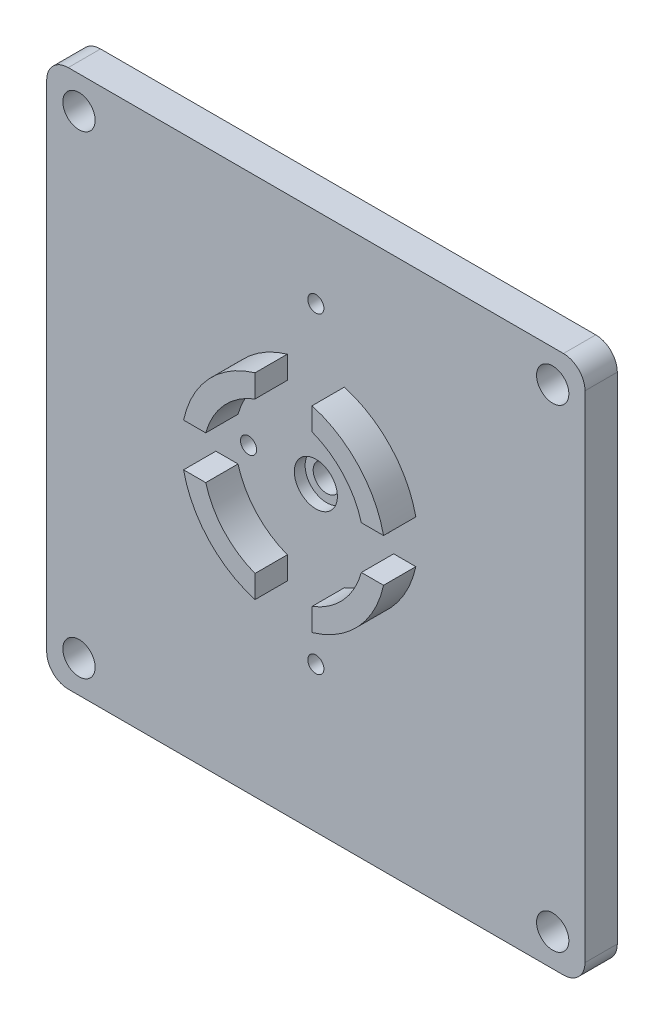
SolidWorks part; units mm, degrees
ref_plane "前视基准面" through (0, 0, 0) normal (0, 0, 1) x (1, 0, 0)
ref_plane "上视基准面" through (0, 0, 0) normal (0, 1, 0) x (1, 0, 0)
ref_plane "右视基准面" through (0, 0, 0) normal (1, 0, 0) x (0, 0, -1)
sketch "草图1" plane through (0, 0, 0) normal (0, 0, 1) x (1, 0, 0)
  line L0 (0, 0) -> (-22, 22) construction
  line L1 (-23, 25) -> (23, 25)
  line L2 (-25, 23) -> (-25, -23)
  line L3 (-23, -25) -> (23, -25)
  line L4 (25, 23) -> (25, -23)
  line L5 (-25, 25) -> (25, -25) construction
  line L6 (-25, -25) -> (25, 25) construction
  circle A0 centre (-22, 22) radius 1.5
  arc A1 (-25, -23) -> (-23, -25) centre (-23, -23) ccw
  arc A2 (23, -25) -> (25, -23) centre (23, -23) ccw
  arc A3 (23, 25) -> (25, 23) centre (23, 23) cw
  arc A4 (-23, 25) -> (-25, 23) centre (-23, 23) ccw
  circle A5 centre (22, 22) radius 1.5
  circle A6 centre (22, -22) radius 1.5
  circle A7 centre (-22, -22) radius 1.5
  point P0 (0, 0)
  dimension "D3" = 3
  dimension "D4" = 3
  dimension "D5" = 2
  dimension "D7" = 3
  dimension "D1" = 50
  dimension "D2" = 50
  dimension "D6" = 4
extrude "凸台-拉伸1" add sketch "草图1" along normal blind 3
sketch "草图2" plane through (0, 0, 3) normal (0, 0, 1) x (1, 0, 0)
  line L1 (-2.65, 14) -> (2.65, 14)
  line L2 (-2.65, 14) -> (-2.65, -8)
  line L3 (-2.65, -8) -> (2.65, -8)
  line L4 (2.65, 14) -> (2.65, -8)
  line L5 (-2.65, 14) -> (2.65, -8) construction
  line L6 (-2.65, -8) -> (2.65, 14) construction
  line L7 (-10, 5) -> (10, 5)
  line L8 (-10, 5) -> (-10, 1)
  line L9 (-10, 1) -> (10, 1)
  line L10 (10, 5) -> (10, 1)
  line L11 (-10, 5) -> (10, 1) construction
  line L12 (-10, 1) -> (10, 5) construction
  circle A0 centre (0, 3) radius 7.5
  circle A1 centre (0, 3) radius 9.5
  dimension "D1" = 3
  dimension "D2" = 15
  dimension "D4" = 5.3
  dimension "D5" = 4
  dimension "D6" = 22
  dimension "D7" = 20
  dimension "D3" = 2
extrude "凸台-拉伸2" add sketch "草图2" along normal blind 3 contours L4 A1 L9 A0 | L9 A1 L2 A0 | L2 A1 L7 A0 | L7 A1 L4 A0
sketch "草图3" plane through (0, 0, 3) normal (0, 0, 1) x (1, 0, 0)
  circle A0 centre (0, 3) radius 1.25
  dimension "D1" = 2.5
  dimension "D2" = 3
extrude "切除-拉伸1" cut sketch "草图3" against normal blind 3
sketch "草图4" plane through (0, 0, 3) normal (0, 0, 1) x (1, 0, 0)
  circle A0 centre (0, 3) radius 14.5 construction
  circle A1 centre (0, 17.5) radius 0.75
  circle A2 centre (0, -11.5) radius 0.75
  circle A3 centre (-6.25, 3) radius 0.75
  circle A4 centre (6.25, 3) radius 0.75
  circle A5 centre (0, 3) radius 1.25 construction
  dimension "D1" = 29
  dimension "D2" = 1.5
  dimension "D3" = 12.5
  dimension "D4" = 6.25
extrude "切除-拉伸2" cut sketch "草图4" against normal blind 10
sketch "草图5" plane through (0, 0, 0) normal (0, 0, -1) x (-1, 0, 0)
  circle A0 centre (0, 3) radius 2
  dimension "D1" = 4
extrude "切除-拉伸3" cut sketch "草图5" along normal blind 1 from surface at -3 starting at face at (0.75, 17.5, 3)
